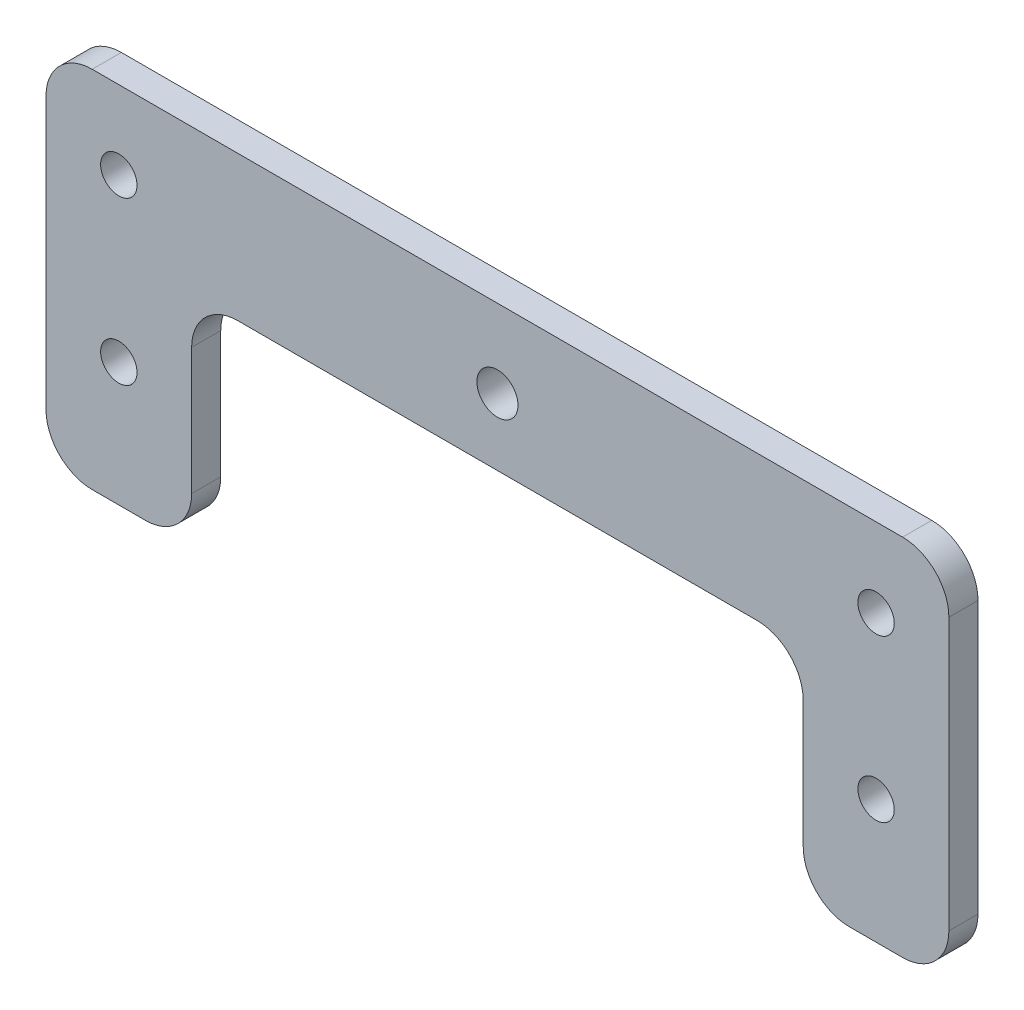
SolidWorks part; units mm, degrees
ref_plane "Alzado" through (0, 0, 0) normal (0, 0, 1) x (1, 0, 0)
ref_plane "Planta" through (0, 0, 0) normal (0, 1, 0) x (1, 0, 0)
ref_plane "Vista lateral" through (0, 0, 0) normal (1, 0, 0) x (0, 0, -1)
sketch "Croquis1" plane through (0, 0, 0) normal (0, 0, 1) x (1, 0, 0)
  line L1 (26.5381, 6.6994) -> (97.8381, 6.6994)
  line L2 (0.1881, 6.6044) -> (0.1881, 20.2544)
  line L3 (6.5381, 26.6044) -> (117.8381, 26.6044)
  line L4 (124.1881, 6.6044) -> (124.1881, 20.2544)
  line L6 (0.1881, 6.6044) -> (0.1881, -17.0456)
  line L7 (6.5381, -23.3956) -> (13.8381, -23.3956)
  line L8 (20.1881, 0.3494) -> (20.1881, -17.0456)
  line L13 (62.1881, 26.6044) -> (62.1881, -35.7819) construction
  line L14 (117.8381, -23.3956) -> (110.5381, -23.3956)
  line L15 (104.1881, 0.3494) -> (104.1881, -17.0456)
  line L16 (124.1881, 6.6044) -> (124.1881, -17.0456)
  circle A1 centre (10.1881, 15.8665) radius 2.5
  circle A2 centre (114.1881, 15.7714) radius 2.5
  circle A3 centre (10.1881, -6.3956) radius 2.5
  arc A5 (26.5381, 6.6994) -> (20.1881, 0.3494) centre (26.5381, 0.3494) ccw
  arc A6 (124.1881, 20.2544) -> (117.8381, 26.6044) centre (117.8381, 20.2544) ccw
  arc A7 (6.5381, 26.6044) -> (0.1881, 20.2544) centre (6.5381, 20.2544) ccw
  arc A8 (104.1881, 0.3494) -> (97.8381, 6.6994) centre (97.8381, 0.3494) ccw
  arc A9 (6.5381, -23.3956) -> (0.1881, -17.0456) centre (6.5381, -17.0456) cw
  arc A10 (13.8381, -23.3956) -> (20.1881, -17.0456) centre (13.8381, -17.0456) ccw
  circle A24 centre (62.1881, 15.8665) radius 2.8214
  arc A30 (117.8381, -23.3956) -> (124.1881, -17.0456) centre (117.8381, -17.0456) ccw
  arc A31 (110.5381, -23.3956) -> (104.1881, -17.0456) centre (110.5381, -17.0456) cw
  circle A32 centre (114.1881, -6.3956) radius 2.5
  point P22 (20.1881, 6.6994)
  point P25 (124.1881, 26.6044)
  point P28 (0.1881, 26.6044)
  point P31 (114.1981, 6.6994)
  point P34 (0.1881, -23.3956)
  point P37 (20.1881, -23.3956)
  dimension "D8" = 5
  dimension "D19" = 6.35
  dimension "D20" = 6.35
  dimension "D21" = 6.35
  dimension "D1" = 20
  dimension "D2" = 124
  dimension "D3" = 30
  dimension "D4" = 20
  dimension "D15" = 10
  dimension "D16" = 10
  dimension "D18" = 94.01
extrude "Saliente-Extruir1" add sketch "Croquis1" along normal blind 4
